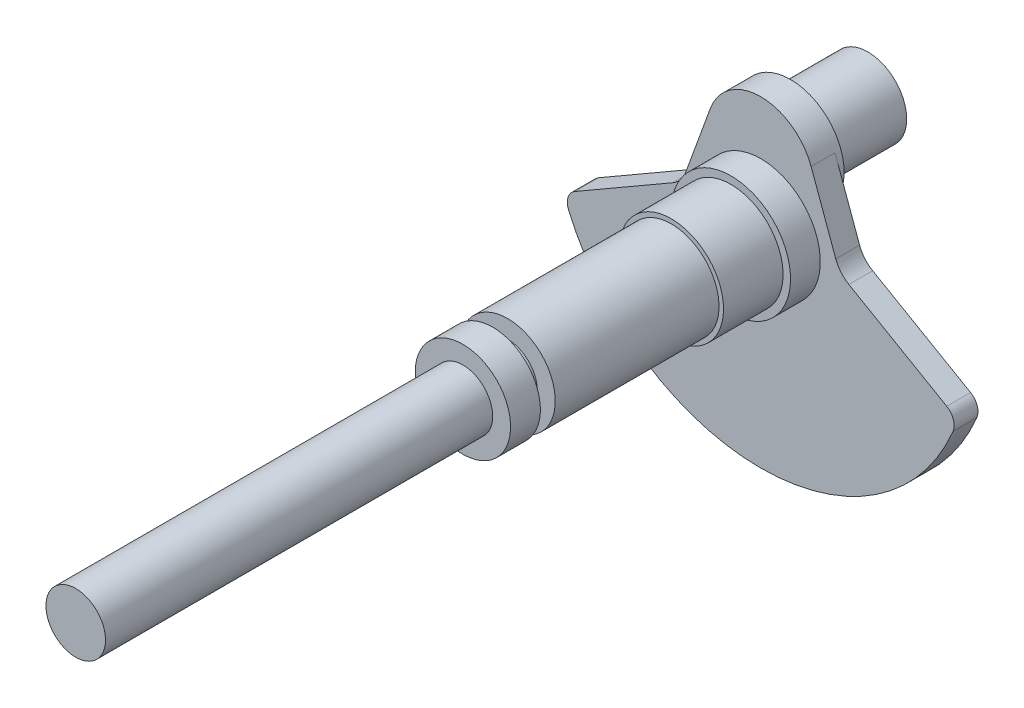
SolidWorks part; units mm, degrees
material "4032-T6"
ref_plane "Front Plane" through (0, 0, 0) normal (0, 0, 1) x (1, 0, 0)
ref_plane "Top Plane" through (0, 0, 0) normal (0, 1, 0) x (1, 0, 0)
ref_plane "Right Plane" through (0, 0, 0) normal (1, 0, 0) x (0, 0, -1)
sketch "Sketch1" plane through (0, 0, 0) normal (0, 0, 1) x (1, 0, 0)
  circle A0 centre (0, 0) radius 10
  dimension "D1" = 20
extrude "Boss-Extrude1" add sketch "Sketch1" against normal blind 130
sketch "Sketch2" plane through (0, 0, -130) normal (0, 0, -1) x (-1, 0, 0)
  circle A0 centre (0, 0) radius 16
  dimension "D1" = 32
extrude "Boss-Extrude2" add sketch "Sketch2" along normal blind 10
sketch "Sketch3" plane through (0, 0, -140) normal (0, 0, -1) x (-1, 0, 0)
  circle A0 centre (0, 0) radius 10
  dimension "D1" = 20
extrude "Boss-Extrude4" add sketch "Sketch3" along normal blind 5
sketch "Sketch6" plane through (0, 0, -145) normal (0, 0, -1) x (-1, 0, 0)
  circle A0 centre (0, 0) radius 16
  dimension "D1" = 32
extrude "Boss-Extrude5" add sketch "Sketch6" along normal blind 55
sketch "Sketch7" plane through (0, 0, -200) normal (0, 0, -1) x (-1, 0, 0)
  circle A0 centre (0, 0) radius 17.5
  dimension "D1" = 35
extrude "Boss-Extrude6" add sketch "Sketch7" along normal blind 20
sketch "Sketch8" plane through (0, 0, -220) normal (0, 0, -1) x (-1, 0, 0)
  circle A0 centre (0, 0) radius 20
  dimension "D1" = 40
extrude "Boss-Extrude7" add sketch "Sketch8" along normal blind 10
sketch "Sketch9" plane through (0, 0, -230) normal (0, 0, -1) x (-1, 0, 0)
  circle A1 centre (0, 0) radius 20
  circle A2 centre (0, 0) radius 20
  circle A3 centre (0, 20) radius 18
  circle M2 centre (0, 0) radius 20
  dimension "D2" = 36
  dimension "D1" = 0
extrude "Boss-Extrude8" add sketch "Sketch9" along normal blind 10 contours A3 M2 | A3 M2
sketch "Sketch10" plane through (0, 0, -240) normal (0, 0, -1) x (-1, 0, 0)
  circle A1 centre (0, 20) radius 13
  dimension "D1" = 26
extrude "Boss-Extrude9" add sketch "Sketch10" along normal blind 26
sketch "Sketch11" plane through (0, 0, -230) normal (0, 0, 1) x (1, 0, 0)
  line L0 (0, 49.155) -> (0, -5.3184) construction
  line L1 (0, -65.5353) -> (0, 65.5353) construction
  line L2 (-43.7824, 20) -> (41.1096, 20) construction
  line L3 (-53.7098, 0) -> (67.9645, 0) construction
  line L4 (-16.9145, 26.1564) -> (-25.1898, 3.4202)
  line L5 (16.9145, 26.1564) -> (25.1898, 3.4202)
  line L6 (-29.5867, -1.8199) -> (-62.4487, -20.7927)
  line L7 (29.5867, -1.8199) -> (62.4487, -20.7927)
  arc A1 (25.1898, 3.4202) -> (29.5867, -1.8199) centre (34.5867, 6.8404) ccw
  arc A3 (-25.1898, 3.4202) -> (-29.5867, -1.8199) centre (-34.5867, 6.8404) cw
  arc A4 (-64.5601, -27.0554) -> (64.5601, -27.0554) centre (0, 0) ccw
  arc A5 (62.4487, -20.7927) -> (64.5601, -27.0554) centre (59.9487, -25.1229) cw
  arc A6 (-64.5601, -27.0554) -> (-62.4487, -20.7927) centre (-59.9487, -25.1229) cw
  arc A7 (-16.9145, 26.1564) -> (16.9145, 26.1564) centre (0, 20) ccw
  point P18 (26.4346, 0)
  point P21 (-26.4346, 0)
  dimension "D4" = 10
  dimension "D5" = 10
  dimension "D6" = 140
  dimension "D7" = 5
  dimension "D8" = 5
  dimension "D1" = 20
  dimension "D2" = 20
  dimension "D3" = 30
extrude "Boss-Extrude10" add sketch "Sketch11" against normal blind 8
